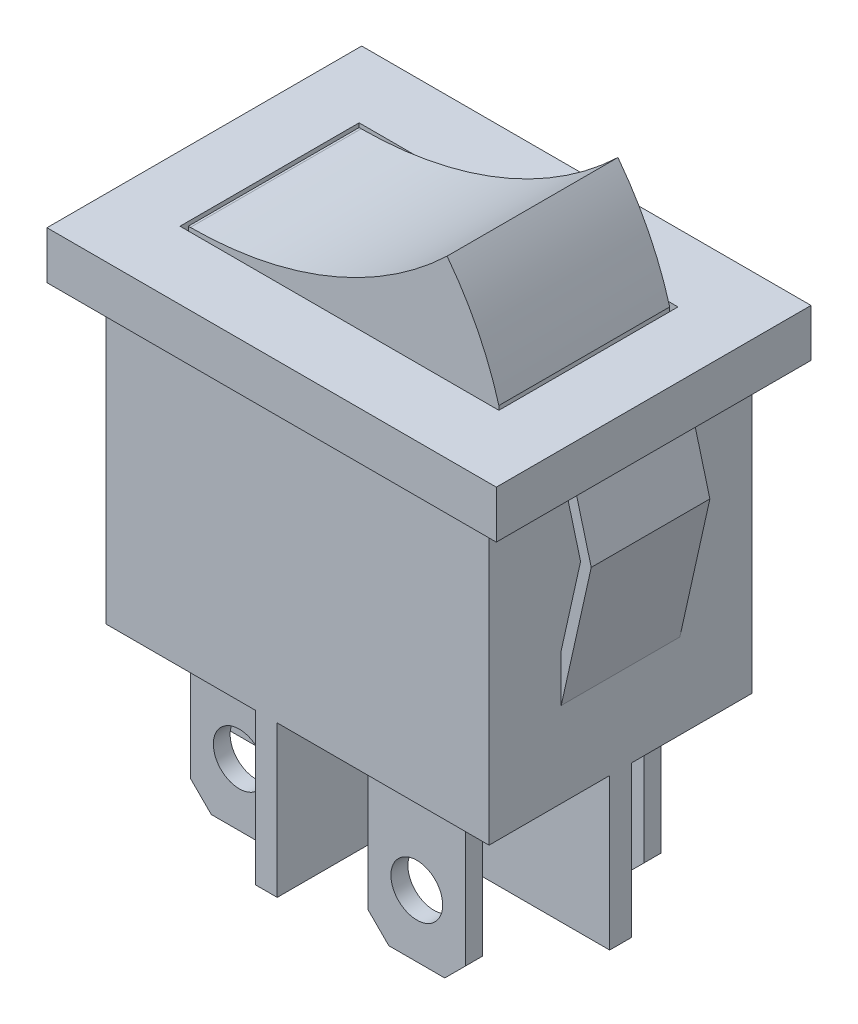
SolidWorks part; units mm, degrees
material "6061 合金"
ref_plane "前视基准面" through (0, 0, 0) normal (0, 0, 1) x (1, 0, 0)
ref_plane "上视基准面" through (0, 0, 0) normal (0, 1, 0) x (1, 0, 0)
ref_plane "右视基准面" through (0, 0, 0) normal (1, 0, 0) x (0, 0, -1)
sketch "草图1" plane through (0, 0, 0) normal (0, 0, 1) x (1, 0, 0)
  line L1 (-9.25, -8.2) -> (9.25, -8.2)
  line L2 (-9.25, -8.2) -> (-9.25, 8.2)
  line L3 (-9.25, 8.2) -> (9.25, 8.2)
  line L4 (9.25, -8.2) -> (9.25, 8.2)
  line L5 (-9.25, -8.2) -> (9.25, 8.2) construction
  line L6 (-9.25, 8.2) -> (9.25, -8.2) construction
  point P0 (0, 0)
  dimension "D1" = 18.5
  dimension "D2" = 16.4
extrude "凸台-拉伸1" add sketch "草图1" along normal mid plane 12.7
sketch "草图2" plane through (0, 8.2, 0) normal (0, 1, 0) x (1, 0, 0)
  line L1 (-10.85, -7.6) -> (10.85, -7.6)
  line L2 (-10.85, -7.6) -> (-10.85, 7.6)
  line L3 (-10.85, 7.6) -> (10.85, 7.6)
  line L4 (10.85, -7.6) -> (10.85, 7.6)
  line L5 (-10.85, -7.6) -> (10.85, 7.6) construction
  line L6 (-10.85, 7.6) -> (10.85, -7.6) construction
  point P0 (0, 0)
  dimension "D1" = 21.7
  dimension "D2" = 15.2
extrude "凸台-拉伸2" add sketch "草图2" against normal blind 2.3
sketch "草图3" plane through (0, 0, 0) normal (0, 0, 1) x (1, 0, 0)
  line L0 (9.25, 5.9) -> (9.7674, 5.9)
  line L1 (-10.85, 5.9) -> (10.85, 5.9) construction
  line L2 (9.7674, 5.9) -> (10.7, 2.4)
  line L3 (10.7, 2.4) -> (9.25, -4.1)
  line L4 (9.25, -8.2) -> (9.25, 5.9) construction
  line L5 (9.25, -4.1) -> (9.25, -1.8035)
  line L6 (9.25, -1.8035) -> (10.1854, 2.3895)
  line L7 (10.1854, 2.3895) -> (9.25, 5.9)
  line L8 (0, 8.6324) -> (0, -9.3432) construction
  line L9 (-10.1854, 2.3895) -> (-9.25, 5.9)
  line L10 (-9.25, -1.8035) -> (-10.1854, 2.3895)
  line L11 (-9.25, -4.1) -> (-9.25, -1.8035)
  line L12 (-10.7, 2.4) -> (-9.25, -4.1)
  line L13 (-9.7674, 5.9) -> (-10.7, 2.4)
  line L14 (-9.25, 5.9) -> (-9.7674, 5.9)
  dimension "D1" = 0.5
  dimension "D2" = 0.5
  dimension "D3" = 3.5
  dimension "D4" = 10
  dimension "D5" = 21.4
extrude "凸台-拉伸3" add sketch "草图3" along normal mid plane 5.73
sketch "草图4" plane through (0, -8.2, 0) normal (0, -1, 0) x (1, 0, 0)
  line L0 (9.25, 6.35) -> (9.25, -6.35) construction
  line L1 (-9.25, 0.525) -> (-2.03, 0.525)
  line L2 (-9.25, 0.525) -> (-9.25, -0.525)
  line L3 (-9.25, -0.525) -> (-2.03, -0.525)
  line L4 (9.25, 0.525) -> (9.25, -0.525)
  line L5 (-9.25, 0.525) -> (9.25, -0.525) construction
  line L6 (-9.25, -0.525) -> (9.25, 0.525) construction
  line L7 (9.25, 6.35) -> (-9.25, 6.35) construction
  line L8 (-9.25, 6.35) -> (-9.25, -6.35) construction
  line L11 (-0.98, 0.525) -> (9.25, 0.525)
  line L12 (-2.03, 0.525) -> (-2.03, 6.35)
  line L13 (-0.98, 0.525) -> (-0.98, 6.35)
  line L14 (-2.03, 6.35) -> (-0.98, 6.35)
  line L15 (-0.98, -0.525) -> (9.25, -0.525)
  line L16 (-2.03, -0.525) -> (-2.03, -6.35)
  line L17 (-0.98, -0.525) -> (-0.98, -6.35)
  line L18 (-2.03, -6.35) -> (-0.98, -6.35)
  point P0 (0, 0)
  dimension "D1" = 1.05
  dimension "D2" = 1.05
  dimension "D3" = 7.22
extrude "凸台-拉伸4" add sketch "草图4" along normal blind 7.3
sketch "草图5" plane through (0, -8.2, 0) normal (0, -1, 0) x (1, 0, 0)
  line L0 (-12.0372, 0) -> (13.6192, 0) construction
  line L1 (-0.98, 6.35) -> (9.25, 6.35) construction
  line L2 (-7.99, 2.715) -> (-3.29, 2.715)
  line L3 (-7.99, 2.715) -> (-7.99, 3.525)
  line L4 (-7.99, 3.525) -> (-3.29, 3.525)
  line L5 (-3.29, 2.715) -> (-3.29, 3.525)
  line L6 (-7.99, 2.715) -> (-3.29, 3.525) construction
  line L7 (-7.99, 3.525) -> (-3.29, 2.715) construction
  line L8 (1.785, 3.905) -> (6.485, 3.905)
  line L9 (1.785, 3.905) -> (1.785, 4.725)
  line L10 (1.785, 4.725) -> (6.485, 4.725)
  line L11 (6.485, 3.905) -> (6.485, 4.725)
  line L12 (1.785, 3.905) -> (6.485, 4.725) construction
  line L13 (1.785, 4.725) -> (6.485, 3.905) construction
  line L14 (-9.25, 6.35) -> (-2.03, 6.35) construction
  line L15 (-2.03, 0.525) -> (-9.25, 0.525) construction
  line L16 (9.25, 0.525) -> (-0.98, 0.525) construction
  line L17 (1.785, -4.725) -> (6.485, -3.905) construction
  line L18 (1.785, -3.905) -> (6.485, -4.725) construction
  line L19 (-7.99, -3.525) -> (-3.29, -2.715) construction
  line L20 (-7.99, -2.715) -> (-3.29, -3.525) construction
  line L21 (6.485, -3.905) -> (6.485, -4.725)
  line L22 (1.785, -4.725) -> (6.485, -4.725)
  line L23 (1.785, -3.905) -> (1.785, -4.725)
  line L24 (1.785, -3.905) -> (6.485, -3.905)
  line L25 (-3.29, -2.715) -> (-3.29, -3.525)
  line L26 (-7.99, -3.525) -> (-3.29, -3.525)
  line L27 (-7.99, -2.715) -> (-7.99, -3.525)
  line L28 (-7.99, -2.715) -> (-3.29, -2.715)
  point P3 (-5.64, 3.12)
  point P8 (4.135, 4.315)
  point P15 (4.135, 6.35)
  point P18 (-5.64, 6.35)
  point P31 (4.135, -4.315)
  point P32 (-5.64, -3.12)
  dimension "D1" = 0.82
  dimension "D2" = 0.81
  dimension "D3" = 4.7
  dimension "D4" = 4.7
  dimension "D5" = 3
  dimension "D6" = 4.2
extrude "凸台-拉伸5" add sketch "草图5" along normal blind 8.25
chamfer "倒角1" distance 1 angle 45 8 edges at (6.485, -16.45, -4.315) (6.485, -16.45, 4.315) (1.785, -16.45, -4.315) (1.785, -16.45, 4.315) (-3.29, -16.45, 3.12) (-3.29, -16.45, -3.12) (-7.99, -16.45, -3.12) (-7.99, -16.45, 3.12)
sketch "草图6" plane through (0, 0, 4.725) normal (0, 0, 1) x (1, 0, 0)
  line L0 (5.485, -16.45) -> (2.785, -16.45) construction
  line L1 (-4.29, -16.45) -> (-6.99, -16.45) construction
  circle A0 centre (4.135, -13.45) radius 1.25
  circle A1 centre (-5.64, -13.45) radius 1.25
  point P4 (4.135, -16.45)
  point P9 (-5.64, -16.45)
  dimension "D1" = 2.5
  dimension "D2" = 2.5
  dimension "D3" = 3
extrude "切除-拉伸1" cut sketch "草图6" against normal blind 2.25
mirror "镜向1" about plane through (0, 0, 0) normal (0, 0, 1) of "切除-拉伸1"
sketch "草图7" plane through (0, 0, 0) normal (0, 0, 1) x (1, 0, 0)
  line L0 (-7.5, 8.2) -> (7.5, 8.2)
  line L1 (-10.85, 8.2) -> (10.85, 8.2) construction
  arc A0 (-7.5, 8.2) -> (5, 13.2) centre (-7.45, 26.1999) ccw
  arc A1 (5, 13.2) -> (7.5, 8.2) centre (-6.9314, 4.1093) cw
  point P4 (0, 8.2)
  dimension "D4" = 18
  dimension "D5" = 15
  dimension "D1" = 15
  dimension "D2" = 5
  dimension "D3" = 2.5
extrude "凸台-拉伸6" add sketch "草图7" along normal mid plane 8.25 contours A1 A0 L0
sketch "草图8" plane through (0, 8.2, 0) normal (0, 1, 0) x (1, 0, 0)
  line L0 (-7.7, -4.325) -> (-7.7, 4.325)
  line L1 (-7.5, -4.125) -> (7.5, -4.125)
  line L2 (-7.5, -4.125) -> (-7.5, 4.125)
  line L3 (-7.5, 4.125) -> (7.5, 4.125)
  line L4 (7.5, -4.125) -> (7.5, 4.125)
  line L5 (-7.5, -4.125) -> (7.5, 4.125) construction
  line L6 (-7.5, 4.125) -> (7.5, -4.125) construction
  line L7 (-7.7, 4.325) -> (7.7, 4.325)
  line L8 (7.7, -4.325) -> (7.7, 4.325)
  line L9 (-7.7, -4.325) -> (7.7, -4.325)
  point P0 (0, 0)
  dimension "D1" = 0.2
extrude "切除-拉伸2" cut sketch "草图8" against normal blind 1
